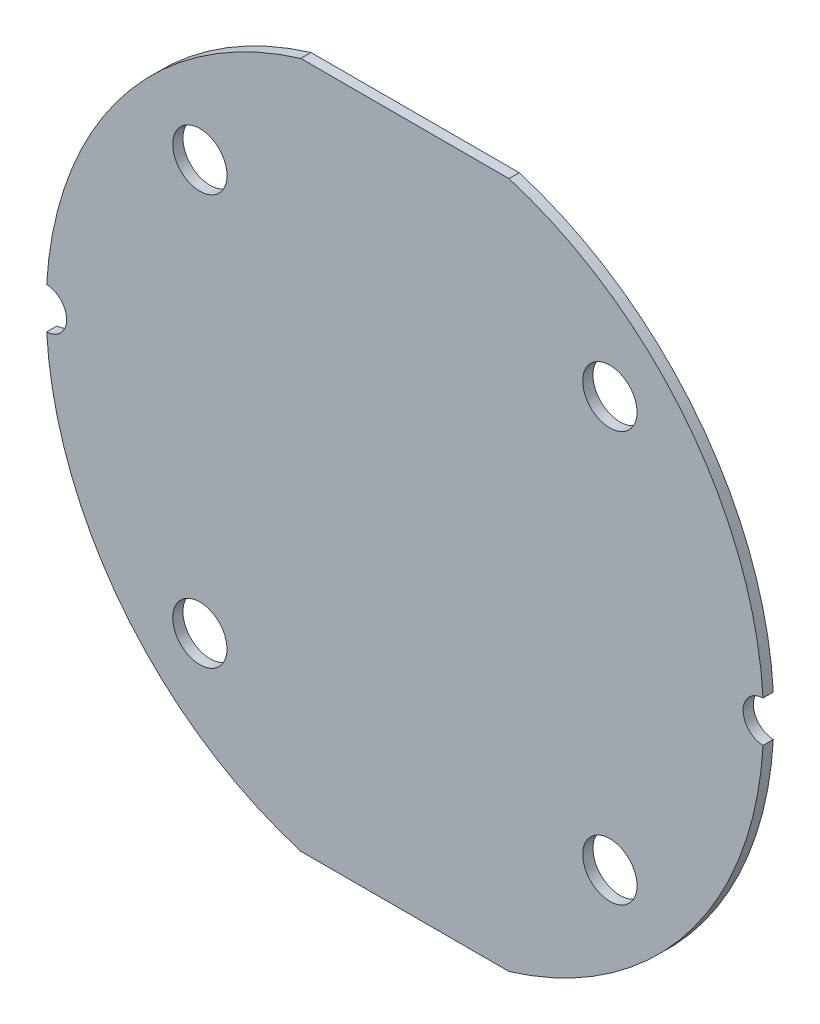
SolidWorks part; units mm, degrees
ref_plane "Front Plane" through (0, 0, 0) normal (0, 0, 1) x (1, 0, 0)
ref_plane "Top Plane" through (0, 0, 0) normal (0, 1, 0) x (1, 0, 0)
ref_plane "Right Plane" through (0, 0, 0) normal (1, 0, 0) x (0, 0, -1)
sketch "Sketch1" plane through (0, 0, 0) normal (0, 0, 1) x (1, 0, 0)
  line L0 (-10.16, 33.4929) -> (10.16, 33.4929)
  line L1 (-35, 0) -> (35, 0) construction
  line L2 (-10.16, -33.4929) -> (10.16, -33.4929)
  line L3 (0, 33.4929) -> (0, -33.4929) construction
  line L4 (-15, 15) -> (-24.7487, 24.7487) construction
  line L5 (-15, 32.5) -> (15, 32.5) construction
  line L6 (-15, 32.5) -> (-15, -32.5) construction
  line L7 (-15, -32.5) -> (15, -32.5) construction
  line L8 (15, 32.5) -> (15, -32.5) construction
  line L9 (-15, 32.5) -> (15, -32.5) construction
  line L10 (-15, -32.5) -> (15, 32.5) construction
  line L11 (-28, 15) -> (-15, 15) construction
  line L12 (-28, 15) -> (-28, -15) construction
  line L13 (-28, -15) -> (-15, -15) construction
  line L14 (-15, 15) -> (-15, -15) construction
  line L15 (-28, 15) -> (-15, -15) construction
  line L16 (-28, -15) -> (-15, 15) construction
  arc A0 (-10.16, 33.4929) -> (-34.9428, 2) centre (0, 0) ccw
  arc A1 (10.16, -33.4929) -> (34.9428, -2) centre (0, 0) ccw
  circle A4 centre (-20, 20) radius 1.65 construction
  circle A6 centre (-20, 20) radius 2.65
  circle A7 centre (-20, -20) radius 2.65
  circle A8 centre (20, -20) radius 2.65
  circle A9 centre (20, 20) radius 2.65
  arc A10 (-34.9428, 2) -> (-34.9428, -2) centre (-35, 0) cw
  arc A11 (34.9428, 2) -> (34.9428, -2) centre (35, 0) ccw
  arc A12 (-34.9428, -2) -> (-10.16, -33.4929) centre (0, 0) ccw
  arc A13 (34.9428, 2) -> (10.16, 33.4929) centre (0, 0) ccw
  point P8 (0, 0)
  point P13 (-21.5, 0)
  point P27 (0, 0)
  point P34 (0, 0)
  dimension "D1" = 70
  dimension "D3" = 65
  dimension "D8" = 3.3
  dimension "D9" = 1
  dimension "D2" = 20.32
  dimension "D4" = 35
  dimension "D5" = 30
  dimension "D6" = 13
  dimension "D7" = 30
  dimension "D10" = 5
  dimension "D11" = 4
extrude "Boss-Extrude1" add sketch "Sketch1" along normal blind 1
